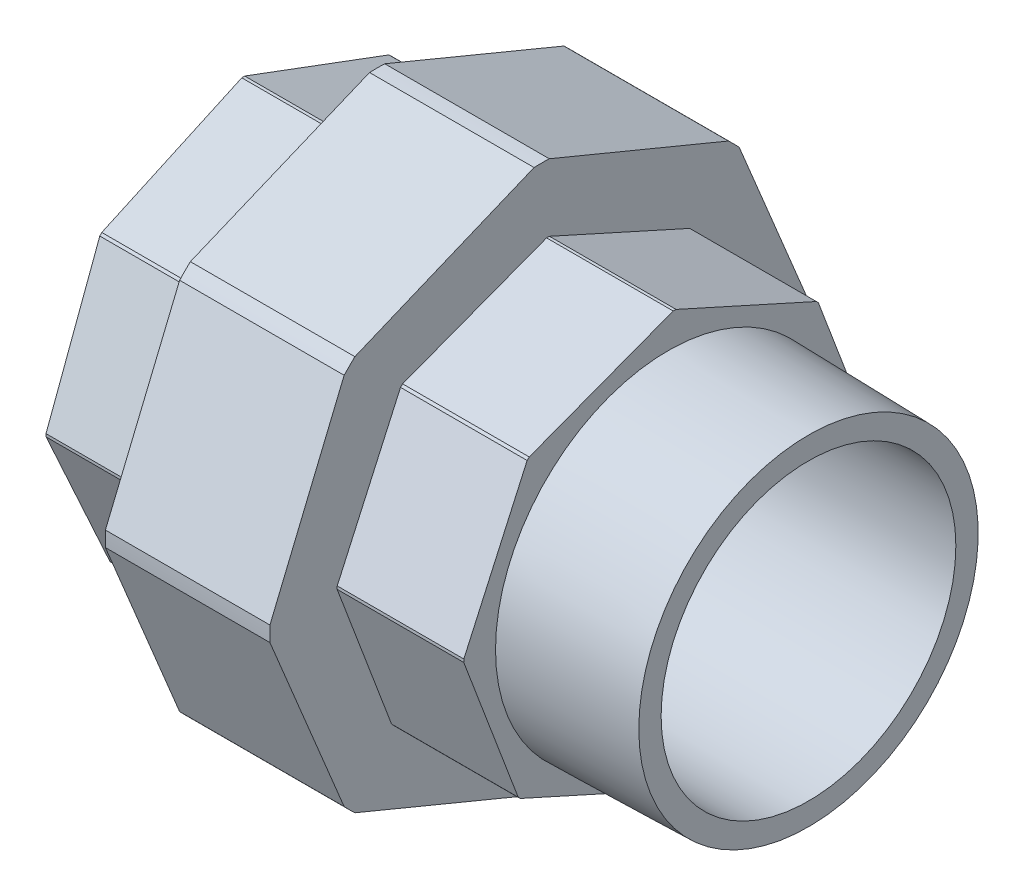
SolidWorks part; units mm, degrees
ref_plane "Front Plane" through (0, 0, 0) normal (0, 0, 1) x (1, 0, 0)
ref_plane "Top Plane" through (0, 0, 0) normal (0, 1, 0) x (1, 0, 0)
ref_plane "Right Plane" through (0, 0, 0) normal (1, 0, 0) x (0, 0, -1)
sketch "Sketch1" plane through (0, 0, 0) normal (0, 0, 1) x (1, 0, 0)
  line L0 (0, -24.15) -> (12.7, -24.15)
  line L1 (12.7, -24.15) -> (12.7, -20.6)
  line L2 (12.7, -20.6) -> (62.8, -20.6)
  line L5 (58.4, -24.15) -> (58.4, -28.6)
  line L6 (58.4, -28.6) -> (40.7, -28.6)
  line L7 (40.7, -28.6) -> (40.7, -38)
  line L8 (40.7, -38) -> (17.7, -38)
  line L9 (17.7, -38) -> (17.7, -28.6)
  line L10 (17.7, -28.6) -> (0, -28.6)
  line L11 (0, -28.6) -> (0, -24.15)
  line L12 (0, 0) -> (36.8378, 0) construction
  line L15 (78, -20.6) -> (62.8, -20.6)
  line L16 (58.4, -24.15) -> (78, -23.7223)
  line L17 (78, -23.7223) -> (78, -20.6)
  dimension "D1" = 20.6
  dimension "D2" = 78
  dimension "D3" = 24.15
  dimension "D4" = 28.6
  dimension "D5" = 12.7
  dimension "D6" = 38
  dimension "D7" = 5
  dimension "D8" = 24.15
  dimension "D9" = 1.25
  dimension "D10" = 23
revolve "Revolve1" add sketch "Sketch1" angle 360 about L12
sketch "Sketch2" plane through (40.7, 0, 0) normal (1, 0, 0) x (0, 0, -1)
  line L7 (0, 38.4249) -> (-27.1705, 27.1705)
  line L8 (-27.1705, 27.1705) -> (-38.4249, 0)
  line L9 (-38.4249, 0) -> (-27.1705, -27.1705)
  line L10 (-27.1705, -27.1705) -> (0, -38.4249)
  line L11 (0, -38.4249) -> (27.1705, -27.1705)
  line L12 (27.1705, -27.1705) -> (38.4249, 0)
  line L13 (38.4249, 0) -> (27.1705, 27.1705)
  line L14 (27.1705, 27.1705) -> (0, 38.4249)
  circle A0 centre (0, 0) radius 35.5 construction
  circle A2 centre (0, 0) radius 66.0096
  dimension "D1" = 71
extrude "Cut-Extrude1" cut sketch "Sketch2" against normal up to surface (23 mm away) up to face at (17.7, 0, 38)
sketch "Sketch4" plane through (0, 0, 0) normal (-1, 0, 0) x (0, 0, 1)
  line L1 (1.0203, 28.6652) -> (-19.5479, 20.9908)
  line L2 (-19.5479, 20.9908) -> (-28.6652, 1.0203)
  line L3 (-28.6652, 1.0203) -> (-20.9908, -19.5479)
  line L4 (-20.9908, -19.5479) -> (-1.0203, -28.6652)
  line L5 (-1.0203, -28.6652) -> (19.5479, -20.9908)
  line L6 (19.5479, -20.9908) -> (28.6652, -1.0203)
  line L7 (28.6652, -1.0203) -> (20.9908, 19.5479)
  line L8 (20.9908, 19.5479) -> (1.0203, 28.6652)
  circle A0 centre (0, 0) radius 26.5 construction
  circle A1 centre (0, 0) radius 31.8562
  dimension "D1" = 53
extrude "Cut-Extrude2" cut sketch "Sketch4" against normal up to surface (17.7 mm away) up to face at (17.7, 0, 28.6)
sketch "Sketch5" plane through (58.4, 0, 0) normal (1, 0, 0) x (0, 0, -1)
  line L1 (0.893, 28.6695) -> (-19.641, 20.9038)
  line L2 (-19.641, 20.9038) -> (-28.6695, 0.893)
  line L3 (-28.6695, 0.893) -> (-20.9038, -19.641)
  line L4 (-20.9038, -19.641) -> (-0.893, -28.6695)
  line L5 (-0.893, -28.6695) -> (19.641, -20.9038)
  line L6 (19.641, -20.9038) -> (28.6695, -0.893)
  line L7 (28.6695, -0.893) -> (20.9038, 19.641)
  line L8 (20.9038, 19.641) -> (0.893, 28.6695)
  circle A0 centre (0, 0) radius 26.5 construction
  circle A1 centre (0, 0) radius 32.9879
  dimension "D1" = 53
extrude "Cut-Extrude3" cut sketch "Sketch5" against normal up to surface (17.7 mm away) up to face at (40.7, 0, 28.6)
